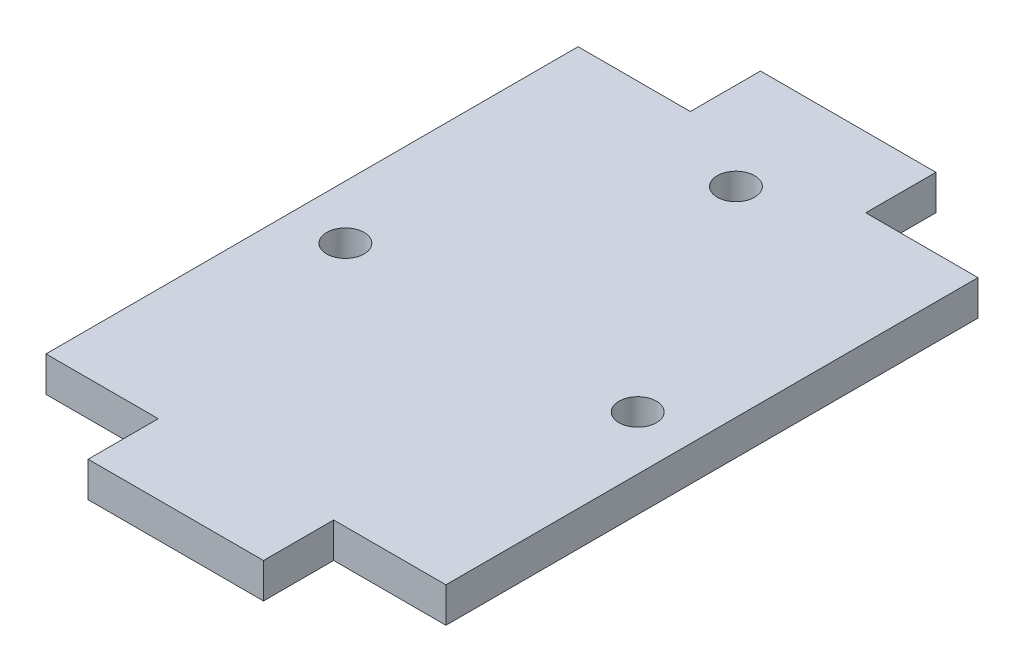
SolidWorks part; units mm, degrees
material "MDF"
ref_plane "Plano frontal" through (0, 0, 0) normal (0, 0, 1) x (1, 0, 0)
ref_plane "Plano superior" through (0, 0, 0) normal (0, 1, 0) x (1, 0, 0)
ref_plane "Plano direito" through (0, 0, 0) normal (1, 0, 0) x (0, 0, -1)
ref_plane "Plano1" through (0, -6, 0) normal (0, -1, 0) x (1, 0, 0)
sketch "Esboço1" plane through (0, -6, 0) normal (0, -1, 0) x (1, 0, 0)
  line L0 (17.1, 41.9) -> (7.5, 41.9)
  line L1 (7.5, 41.9) -> (7.5, 47.9)
  line L2 (7.5, 47.9) -> (-7.5, 47.9)
  line L3 (-7.5, 47.9) -> (-7.5, 41.9)
  line L4 (-7.5, 41.9) -> (-17.1, 41.9)
  line L5 (-17.1, 41.9) -> (-17.1, -3.6)
  line L6 (-17.1, -3.6) -> (-7.5, -3.6)
  line L7 (-7.5, -3.6) -> (-7.5, -9.6)
  line L8 (-7.5, -9.6) -> (7.5, -9.6)
  line L9 (7.5, -9.6) -> (7.5, -3.6)
  line L10 (7.5, -3.6) -> (17.1, -3.6)
  line L11 (17.1, -3.6) -> (17.1, 41.9)
  line L12 (-12.5, 20.9) -> (12.5, 20.9) construction
  line L13 (-7.5, 41.9) -> (7.5, 41.9) construction
  circle A0 centre (-12.5, 20.9) radius 1.6
  circle A1 centre (0, 0) radius 1.6
  circle A2 centre (12.5, 20.9) radius 1.6
  point P18 (0, 20.9)
  point P19 (0, 41.9)
  dimension "D5" = 3.2
  dimension "D1" = 25
  dimension "D2" = 21
  dimension "D3" = 6
  dimension "D4" = 15
  dimension "D6" = 20.9
  dimension "D7" = 34.2
  dimension "D8" = 3.6
extrude "Ressalto-extrusão1" add sketch "Esboço1" against normal blind 3
